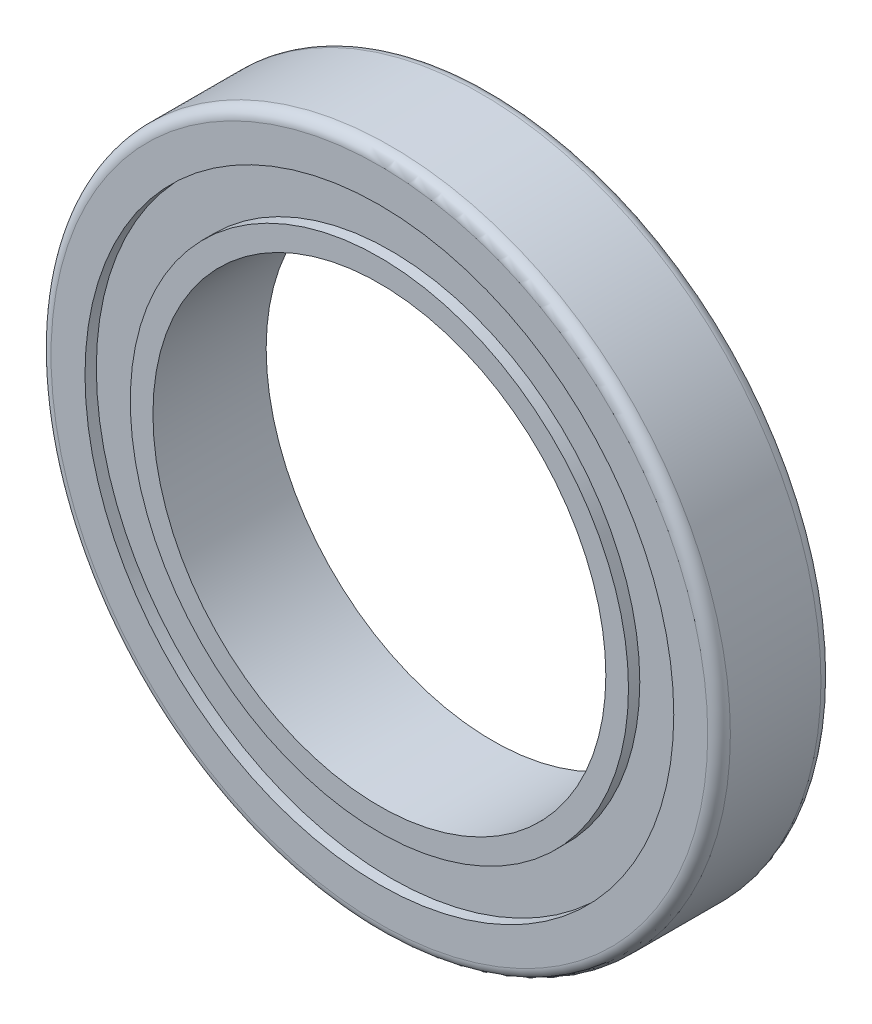
SolidWorks part; units mm, degrees
ref_plane "Front Plane" through (0, 0, 0) normal (0, 0, 1) x (1, 0, 0)
ref_plane "Top Plane" through (0, 0, 0) normal (0, 1, 0) x (1, 0, 0)
ref_plane "Right Plane" through (0, 0, 0) normal (1, 0, 0) x (0, 0, -1)
sketch "Sketch1" plane through (0, 0, 0) normal (0, 0, 1) x (1, 0, 0)
  circle A0 centre (0, 1.5842) radius 10
  circle A1 centre (0, 1.5842) radius 15
extrude "Boss-Extrude1" add sketch "Sketch1" along normal blind 5
fillet "Fillet1" radius 0.5 2 edges at (15, 1.5842, 0) (15, 1.5842, 5)
sketch "Sketch2" plane through (0, 0, 5) normal (0, 0, 1) x (1, 0, 0)
  circle A0 centre (0, 1.5842) radius 13
  circle A1 centre (0, 1.5842) radius 11
extrude "Cut-Extrude1" cut sketch "Sketch2" against normal blind 0.5
sketch "Sketch3" plane through (0, 0, 0) normal (0, 0, -1) x (-1, 0, 0)
  circle A4 centre (0, 1.5842) radius 11 construction
  circle A5 centre (0, 1.5842) radius 13
  circle A6 centre (0, 1.5842) radius 13
  circle A7 centre (0, 1.5842) radius 11
  dimension "D1" = 0
extrude "Cut-Extrude2" cut sketch "Sketch3" against normal blind 0.5
